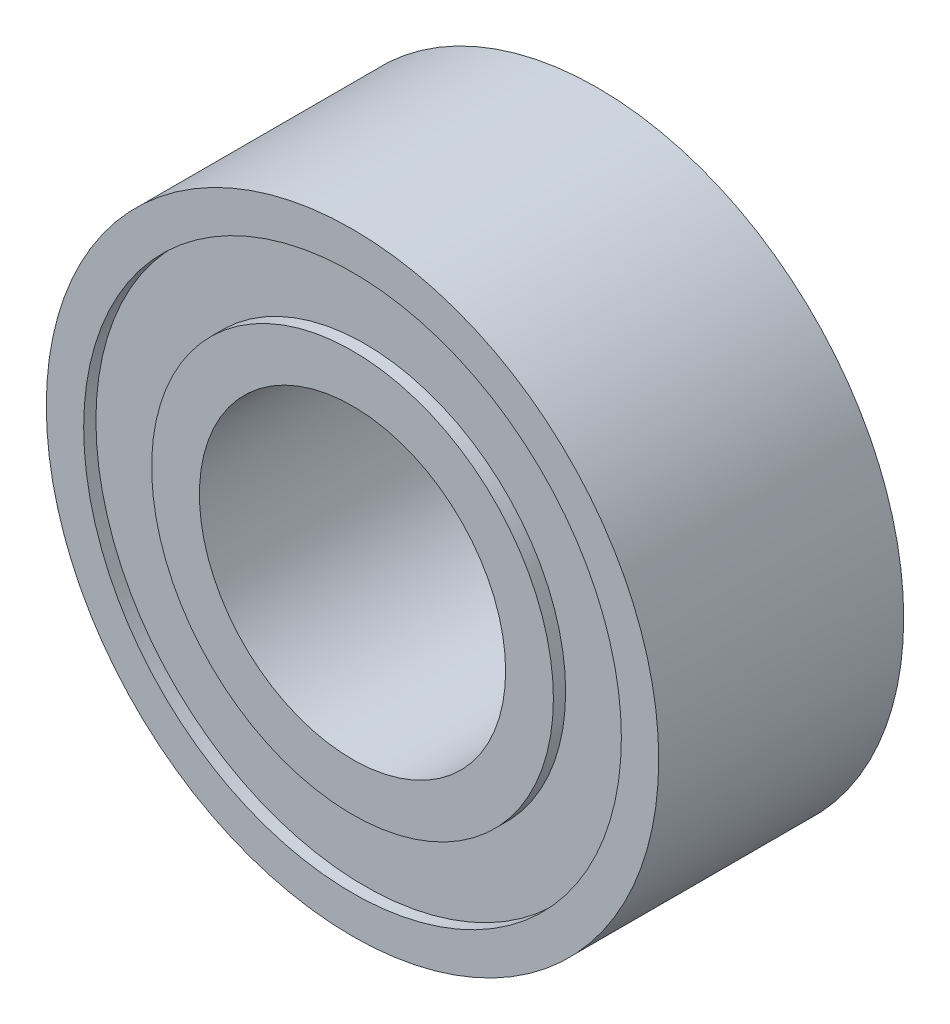
SolidWorks part; units mm, degrees
ref_plane "Front Plane" through (0, 0, 0) normal (0, 0, 1) x (1, 0, 0)
ref_plane "Top Plane" through (0, 0, 0) normal (0, 1, 0) x (1, 0, 0)
ref_plane "Right Plane" through (0, 0, 0) normal (1, 0, 0) x (0, 0, -1)
sketch "Sketch1" plane through (0, 0, 0) normal (0, 0, 1) x (1, 0, 0)
  circle A0 centre (0, 0) radius 5
  circle A1 centre (0, 0) radius 2.5
  dimension "D1" = 10
  dimension "D2" = 5
extrude "Boss-Extrude1" add sketch "Sketch1" along normal mid plane 4
sketch "Sketch2" plane through (0, 0, 2) normal (0, 0, 1) x (1, 0, 0)
  circle A2 centre (0, 0) radius 4.39
  circle A3 centre (0, 0) radius 4.39
  circle A5 centre (0, 0) radius 3.28
  circle A6 centre (0, 0) radius 3.28
  dimension "D1" = 0.61
  dimension "D2" = 0.78
extrude "Cut-Extrude1" cut sketch "Sketch2" against normal blind 0.2
mirror "Mirror1" about plane through (0, 0, 0) normal (0, 0, 1) of "Cut-Extrude1"
